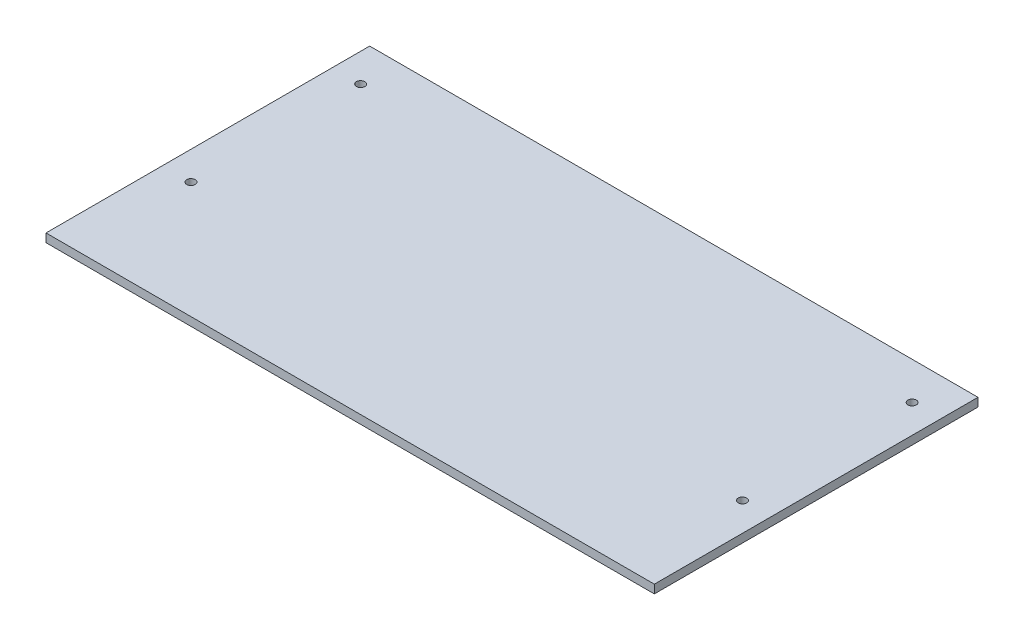
SolidWorks part; units mm, degrees
ref_plane "Alzado" through (0, 0, 0) normal (0, 0, 1) x (1, 0, 0)
ref_plane "Planta" through (0, 0, 0) normal (0, 1, 0) x (1, 0, 0)
ref_plane "Vista lateral" through (0, 0, 0) normal (1, 0, 0) x (0, 0, -1)
sketch "Croquis1" plane through (0, 0, 0) normal (0, 1, 0) x (1, 0, 0)
  line L0 (0, -64.092) -> (0, 101.4115) construction
  line L1 (-97.495, 77.0727) -> (97.495, 77.0727) construction
  line L2 (-107.545, 90.3124) -> (107.545, 90.3124)
  line L3 (-107.545, 90.3124) -> (-107.545, -24.1234)
  line L4 (-107.545, -24.1234) -> (107.545, -24.1234)
  line L5 (107.545, -24.1234) -> (107.545, 90.3124)
  circle A0 centre (-97.495, 77.0727) radius 1.5
  circle A1 centre (97.495, 77.0727) radius 1.5
  circle A2 centre (-97.495, 17.0727) radius 1.5
  circle A3 centre (97.495, 17.0727) radius 1.5
  point P6 (0, 77.0727)
  point P15 (0, 90.3124)
  dimension "D1" = 194.99
  dimension "D2" = 2
  dimension "D3" = 215.09
extrude "Saliente-Extruir1" add sketch "Croquis1" along normal blind 3
